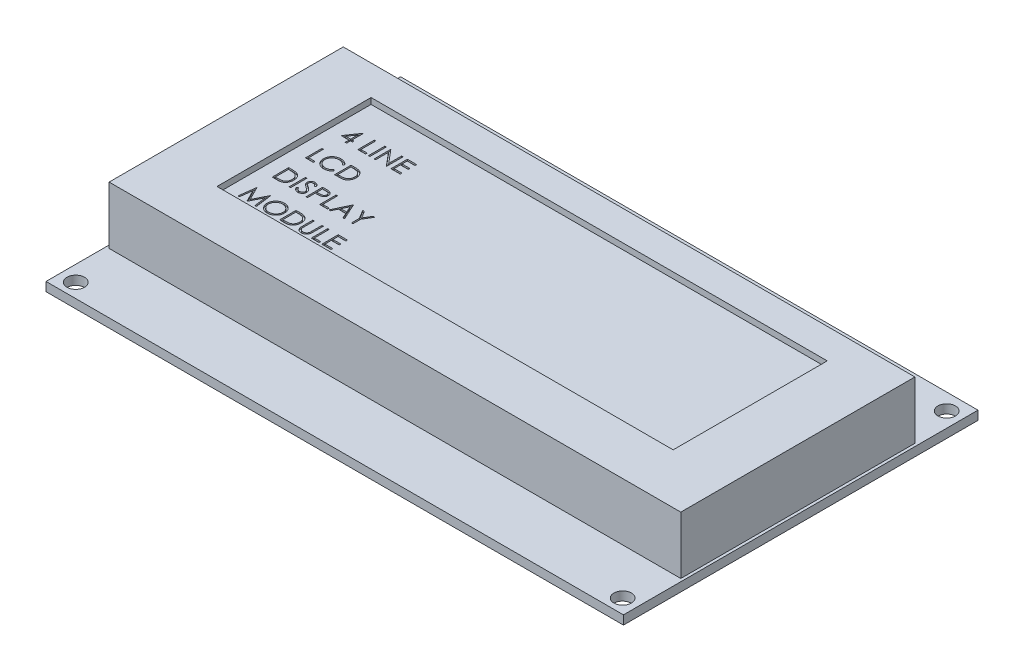
SolidWorks part; units mm, degrees
ref_plane "Front Plane" through (0, 0, 0) normal (0, 0, 1) x (1, 0, 0)
ref_plane "Top Plane" through (0, 0, 0) normal (0, 1, 0) x (1, 0, 0)
ref_plane "Right Plane" through (0, 0, 0) normal (1, 0, 0) x (0, 0, -1)
sketch "Sketch1" plane through (0, 0, 0) normal (0, 1, 0) x (1, 0, 0)
  line L1 (48.53, -19.875) -> (-48.53, -19.875)
  line L2 (48.53, -19.875) -> (48.53, 19.875)
  line L3 (48.53, 19.875) -> (-48.53, 19.875)
  line L4 (-48.53, -19.875) -> (-48.53, 19.875)
  line L5 (48.53, -19.875) -> (-48.53, 19.875) construction
  line L6 (48.53, 19.875) -> (-48.53, -19.875) construction
  point P0 (0, 0)
  dimension "D1" = 97.06
  dimension "D2" = 39.75
extrude "Boss-Extrude1" add sketch "Sketch1" along normal blind 9.76
sketch "Sketch3" plane through (0, 0, 0) normal (0, -1, 0) x (1, 0, 0)
  line L0 (-48.53, -19.875) -> (-48.53, 19.875) construction
  line L1 (49.006, 30.0868) -> (-49.038, 30.0868)
  line L2 (49.006, 30.0868) -> (49.006, -30.1112)
  line L3 (49.006, -30.1112) -> (-49.038, -30.1112)
  line L4 (-49.038, 30.0868) -> (-49.038, -30.1112)
  line L5 (49.006, 30.0868) -> (-49.038, -30.1112) construction
  line L6 (49.006, -30.1112) -> (-49.038, 30.0868) construction
  line L7 (48.53, -19.875) -> (-48.53, -19.875) construction
  point P0 (-0.016, -0.0122)
  point P5 (-48.53, 0)
  dimension "D1" = 60.198
  dimension "D2" = 98.044
  dimension "D3" = 0.508
  dimension "D4" = 10.2362
extrude "Boss-Extrude2" add sketch "Sketch3" along normal blind 1.51
sketch "Sketch7" plane through (0, 9.76, 0) normal (0, 1, 0) x (1, 0, 0)
  line L0 (48.53, 19.875) -> (-48.53, 19.875) construction
  line L1 (-38.7256, 14.795) -> (38.7256, 14.795)
  line L2 (-38.7256, 14.795) -> (-38.7256, -11.367)
  line L3 (-38.7256, -11.367) -> (38.7256, -11.367)
  line L4 (38.7256, 14.795) -> (38.7256, -11.367)
  line L5 (-38.7256, 14.795) -> (38.7256, -11.367) construction
  line L6 (-38.7256, -11.367) -> (38.7256, 14.795) construction
  line L7 (-48.53, 19.875) -> (-48.53, -19.875) construction
  line L8 (48.53, -19.875) -> (48.53, 19.875) construction
  point P0 (0, 1.714)
  dimension "D1" = 26.162
  dimension "D2" = 5.08
  dimension "D3" = 9.8044
  dimension "D4" = 9.8044
extrude "Cut-Extrude3" cut sketch "Sketch7" against normal blind 1.016
sketch "Sketch4" plane through (0, 0, 0) normal (0, 1, 0) x (1, 0, 0)
  line L0 (-49.038, -30.0868) -> (-49.038, 30.1112) construction
  line L1 (-46.394, 27.3342) -> (46.4684, 27.3342) construction
  line L2 (-46.394, 27.3342) -> (-46.394, -27.6822) construction
  line L3 (-46.394, -27.6822) -> (46.4684, -27.6822) construction
  line L4 (46.4684, 27.3342) -> (46.4684, -27.6822) construction
  line L5 (-49.038, 30.1112) -> (49.006, 30.1112) construction
  circle A0 centre (-46.394, 27.3342) radius 1.4859
  circle A1 centre (46.4684, 27.3342) radius 1.4859
  circle A2 centre (46.4684, -27.6822) radius 1.4859
  circle A3 centre (-46.394, -27.6822) radius 1.4859
  dimension "D1" = 2.9718
  dimension "D2" = 92.8624
  dimension "D3" = 55.0164
  dimension "D4" = 2.644
  dimension "D5" = 2.777
extrude "Cut-Extrude1" cut sketch "Sketch4" against normal through all
sketch "Sketch5" plane through (0, 8.744, 0) normal (0, 1, 0) x (1, 0, 0)
  text T0 "4 LINE \r\nLCD\r\nDISPLAY\r\nMODULE\r\n" font "Century Gothic" height 2.794
extrude "Cut-Extrude2" cut sketch "Sketch5" against normal blind 0.254
sketch "Sketch6" plane through (0, -1.51, 0) normal (0, -1, 0) x (1, 0, 0)
  line L0 (-49.038, 30.0868) -> (-49.038, -30.1112) construction
  line L1 (-40.656, -28.4602) -> (0.746, -28.4602)
  line L2 (-40.656, -28.4602) -> (-40.656, -25.9202)
  line L3 (-40.656, -25.9202) -> (0.746, -25.9202)
  line L4 (0.746, -28.4602) -> (0.746, -25.9202)
  line L5 (-49.038, -30.1112) -> (49.006, -30.1112) construction
  dimension "D1" = 2.54
  dimension "D2" = 41.402
  dimension "D3" = 8.382
  dimension "D4" = 4.191
extrude "Boss-Extrude3" add sketch "Sketch6" along normal blind 0.0254
